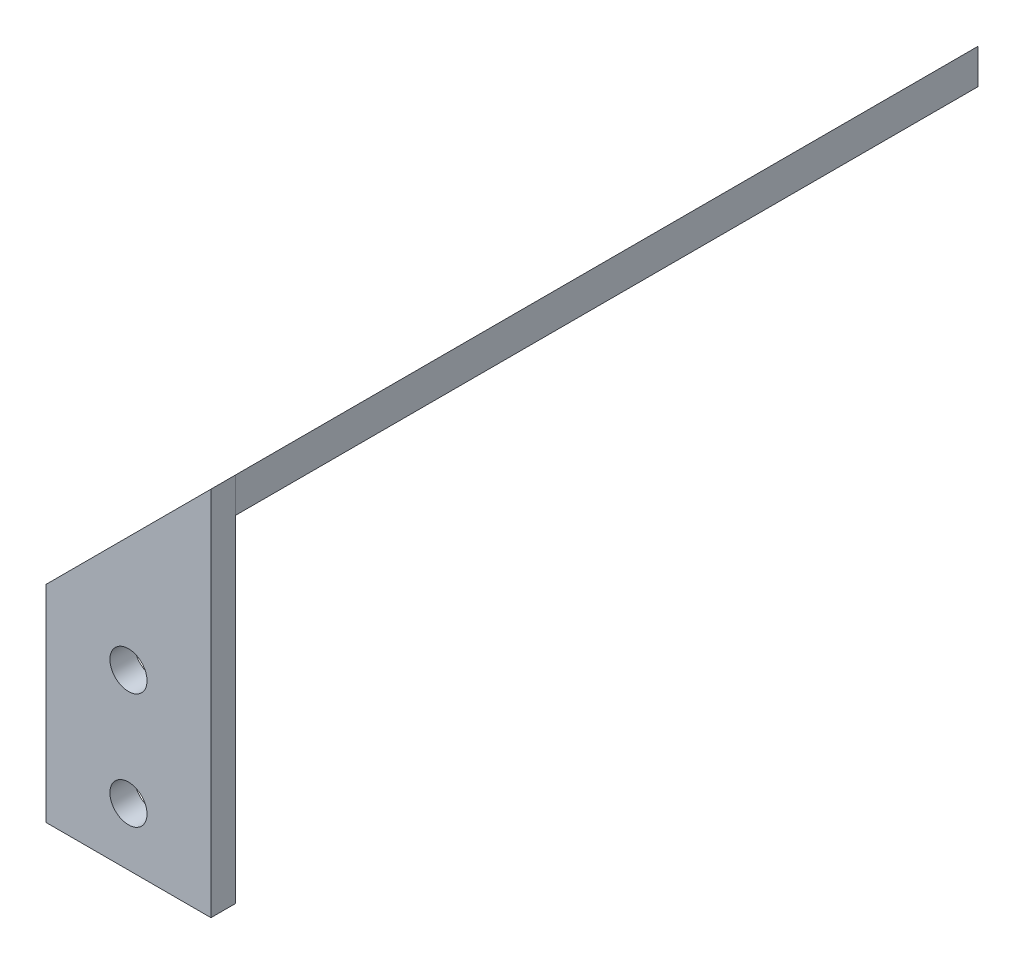
SolidWorks part; units mm, degrees
ref_plane "Front Plane" through (0, 0, 0) normal (0, 0, 1) x (1, 0, 0)
ref_plane "Top Plane" through (0, 0, 0) normal (0, 1, 0) x (1, 0, 0)
ref_plane "Right Plane" through (0, 0, 0) normal (1, 0, 0) x (0, 0, -1)
sketch "Sketch1" plane through (0, 0, 0) normal (0, 0, 1) x (1, 0, 0)
  line L0 (10, 25) -> (10, 0) construction
  line L1 (0, 0) -> (20, 0)
  line L2 (0, 0) -> (0, 25)
  line L4 (20, 0) -> (20, 25)
  line L5 (0, 25) -> (20, 45)
  line L6 (20, 45) -> (20, 25)
  line L7 (20, 25) -> (0, 25) construction
  circle A0 centre (10, 7) radius 2.25
  circle A1 centre (10, 21) radius 2.25
  dimension "D3" = 4.5
  dimension "D1" = 25
  dimension "D2" = 20
  dimension "D4" = 135
  dimension "D5" = 7
  dimension "D6" = 14
extrude "Boss-Extrude1" add sketch "Sketch1" along normal blind 3
sketch "Sketch2" plane through (-12.5, 12.5, 0) normal (-0.7071, 0.7071, 0) x (0, 0, 1)
  line L0 (3, 17.6777) -> (0, 17.6777) construction
  line L1 (0, 45.9619) -> (-90, 45.9619)
  line L2 (0, 45.9619) -> (0, 17.6777)
  line L3 (0, 17.6777) -> (-90, 17.6777)
  line L4 (-90, 45.9619) -> (-90, 17.6777)
  line L5 (-80, 45.9619) -> (-80, 17.6777) construction
  line L6 (-30, 45.9619) -> (-30, 17.6777) construction
  circle A0 centre (-80, 31.8198) radius 2.25
  circle A1 centre (-30, 31.8198) radius 2.25
  dimension "D2" = 4.5
  dimension "D1" = 90
  dimension "D3" = 10
  dimension "D4" = 50
extrude "Boss-Extrude2" add sketch "Sketch2" against normal blind 3 separate body
sketch "Sketch3" plane through (0, 0, 0) normal (0, 0, 1) x (1, 0, 0)
  line L0 (22.1213, 42.8787) -> (20, 45)
  line L1 (20, 45) -> (20, 40.7574)
  line L2 (2.1213, 22.8787) -> (22.1213, 42.8787) construction
  line L3 (22.1213, 42.8787) -> (20, 40.7574)
  dimension "D1" = 45
extrude "Cut-Extrude1" cut sketch "Sketch3" against normal through all
